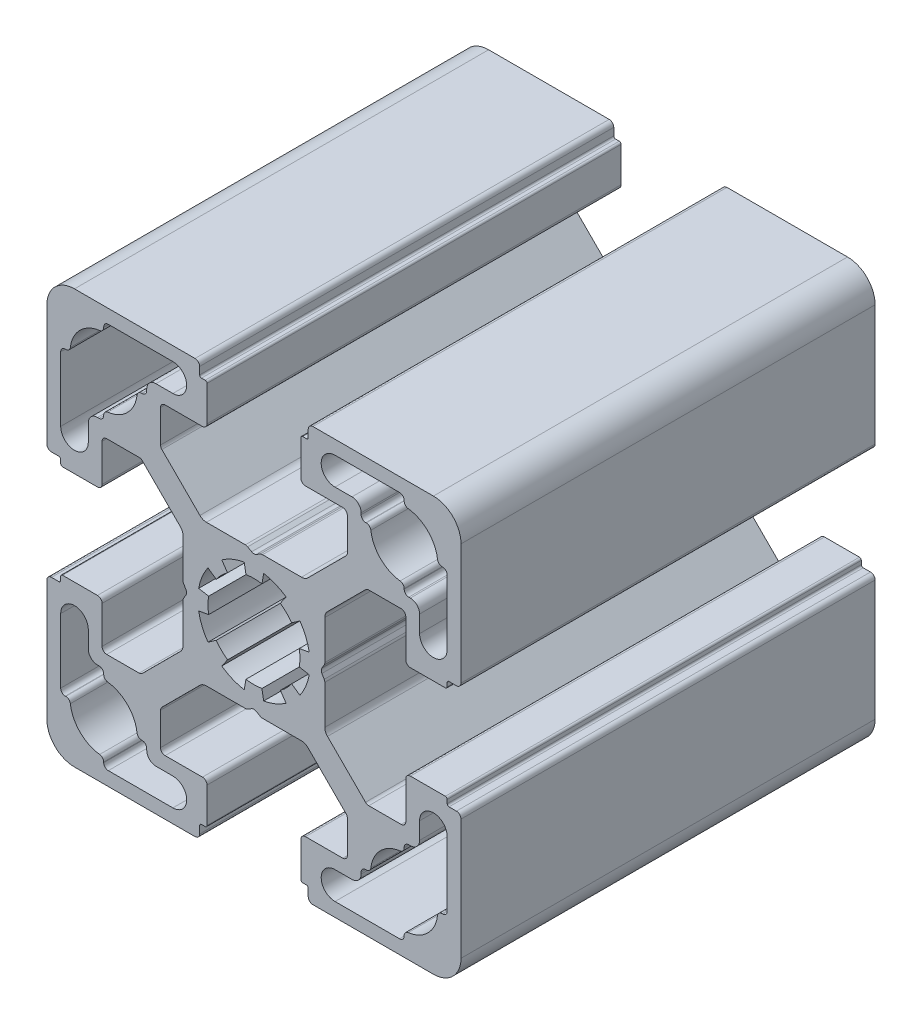
SolidWorks part; units mm, degrees
material "АД31Т ГОСТ 4784-97"
ref_plane "Спереди" through (0, 0, 0) normal (0, 0, 1) x (1, 0, 0)
ref_plane "Сверху" through (0, 0, 0) normal (0, 1, 0) x (1, 0, 0)
ref_plane "Справа" through (0, 0, 0) normal (1, 0, 0) x (0, 0, -1)
sketch "Эскиз1" plane through (0, 0, 0) normal (0, 0, 1) x (1, 0, 0)
  line L0 (-21, 15.825) -> (-21, 8.808)
  line L1 (-15.825, -21) -> (-8.808, -21)
  line L2 (-7.7005, 0.9291) -> (-7.7005, 5.1649)
  line L4 (15.825, 21) -> (8.808, 21)
  line L5 (5.6, 16.5) -> (9.65, 16.5)
  line L6 (16.325, 20.4448) -> (16.325, 20.5)
  line L7 (10.65, 18) -> (8.808, 18)
  line L8 (-7.3858, -0.25) -> (-7.618, -0.6523)
  line L9 (-2.8679, 4.0958) -> (-3.4988, 4.9968)
  line L10 (-16.5, 5.6) -> (-16.5, 9.65)
  line L11 (-16, 10.15) -> (-12.4784, 10.15)
  line L12 (-22, 5.9) -> (-21.2, 5.9)
  line L13 (-20.8, 5.1) -> (-17, 5.1)
  line L14 (-21, 5.7) -> (-21, 5.3)
  line L15 (-22, 5.9) -> (-21.2, 5.9)
  line L16 (4.0958, 2.8679) -> (4.9968, 3.4988)
  line L17 (4.0958, 2.8679) -> (4.9968, 3.4988)
  line L18 (-21, 5.7) -> (-21, 5.3)
  line L19 (-8.1188, 10.2401) -> (-5.8721, 7.9934)
  line L20 (0.9291, 7.7005) -> (5.1649, 7.7005)
  line L21 (-22.5, 6.4) -> (-22.5, 19.5)
  line L22 (10.15, 16) -> (10.15, 12.4784)
  line L23 (0.25, 7.3858) -> (0.6791, 7.6335)
  line L24 (16.325, 12.2052) -> (16.325, 12.15)
  line L25 (-6.4, 22.5) -> (-19.5, 22.5)
  line L26 (16.825, 11.65) -> (17, 11.65)
  line L27 (-10.2401, 8.1188) -> (-12.1249, 10.0036)
  line L28 (-5.7, 21) -> (-5.3, 21)
  line L29 (-7.3858, 0.25) -> (-7.6335, 0.6791)
  line L30 (-0.25, 7.3858) -> (-0.6791, 7.6335)
  line L31 (-5.9, 22) -> (-5.9, 21.2)
  line L32 (-5.7, 21) -> (-5.3, 21)
  line L33 (-5.1, 20.8) -> (-5.1, 17)
  line L34 (-5.9, 22) -> (-5.9, 21.2)
  line L35 (-8.1188, 10.2401) -> (-10.0036, 12.1249)
  line L36 (-5.6, 16.5) -> (-9.65, 16.5)
  line L37 (-10.2401, 8.1188) -> (-7.9934, 5.8721)
  line L38 (18, 10.65) -> (18, 8.808)
  line L39 (-12.2052, 16.325) -> (-12.15, 16.325)
  line L40 (-20.4448, 16.325) -> (-20.5, 16.325)
  line L41 (11.65, 16.825) -> (11.65, 17)
  line L42 (-11.65, 16.825) -> (-11.65, 17)
  line L43 (-18, 10.65) -> (-18, 8.808)
  line L44 (-16.825, 11.65) -> (-17, 11.65)
  line L45 (20.4448, 16.325) -> (20.5, 16.325)
  line L46 (-16.325, 12.2052) -> (-16.325, 12.15)
  line L47 (12.2052, 16.325) -> (12.15, 16.325)
  line L48 (10.2401, 8.1188) -> (7.9934, 5.8721)
  line L49 (0.25, 7.3858) -> (0.6523, 7.618)
  line L50 (-0.9291, 7.7005) -> (-5.1649, 7.7005)
  line L51 (5.6, 16.5) -> (9.65, 16.5)
  line L52 (8.1188, 10.2401) -> (10.0036, 12.1249)
  line L53 (5.9, 22) -> (5.9, 21.2)
  line L54 (5.1, 20.8) -> (5.1, 17)
  line L55 (-0.9291, -7.7005) -> (-5.1649, -7.7005)
  line L56 (5.7, 21) -> (5.3, 21)
  line L57 (5.9, 22) -> (5.9, 21.2)
  line L58 (-0.25, -7.3858) -> (-0.6791, -7.6335)
  line L59 (5.7, 21) -> (5.3, 21)
  line L60 (10.2401, 8.1188) -> (12.1249, 10.0036)
  line L61 (6.4, 22.5) -> (19.5, 22.5)
  line L62 (22.5, 6.4) -> (22.5, 19.5)
  line L63 (-10.15, 16) -> (-10.15, 12.4784)
  line L64 (8.1188, 10.2401) -> (5.8721, 7.9934)
  line L65 (0.25, -7.3858) -> (0.6791, -7.6335)
  line L66 (21, 5.7) -> (21, 5.3)
  line L67 (-0.25, -7.3858) -> (-0.6523, -7.618)
  line L68 (22, 5.9) -> (21.2, 5.9)
  line L69 (21, 5.7) -> (21, 5.3)
  line L70 (20.8, 5.1) -> (17, 5.1)
  line L71 (22, 5.9) -> (21.2, 5.9)
  line L72 (16, 10.15) -> (12.4784, 10.15)
  line L73 (16.5, 5.6) -> (16.5, 9.65)
  line L74 (-0.9291, 7.7005) -> (-5.1649, 7.7005)
  line L75 (2.8679, 4.0958) -> (3.4988, 4.9968)
  line L76 (7.7005, 0.9291) -> (7.7005, 5.1649)
  line L77 (0.9291, -7.7005) -> (5.1649, -7.7005)
  line L78 (21, 15.825) -> (21, 8.808)
  line L79 (-5.6, -16.5) -> (-9.65, -16.5)
  line L80 (-16.325, -20.4448) -> (-16.325, -20.5)
  line L81 (4.0958, -2.8679) -> (4.9968, -3.4988)
  line L82 (2.8679, -4.0958) -> (3.4988, -4.9968)
  line L83 (-10.65, -18) -> (-8.808, -18)
  line L84 (4.0958, -2.8679) -> (4.9968, -3.4988)
  line L85 (2.8679, -4.0958) -> (3.4988, -4.9968)
  line L86 (0.8682, -4.924) -> (1.0593, -6.0073)
  line L87 (0.8682, -4.924) -> (1.0593, -6.0073)
  line L88 (-0.8682, -4.924) -> (-1.0593, -6.0073)
  line L89 (-4.0958, -2.8679) -> (-4.9968, -3.4988)
  line L90 (-0.8682, -4.924) -> (-1.0593, -6.0073)
  line L91 (-4.0958, -2.8679) -> (-4.9968, -3.4988)
  line L92 (21, -15.825) -> (21, -8.808)
  line L93 (2.8679, -4.0958) -> (3.4988, -4.9968)
  line L94 (-0.9291, -7.7005) -> (-5.1649, -7.7005)
  line L95 (16.5, -5.6) -> (16.5, -9.65)
  line L96 (16, -10.15) -> (12.4784, -10.15)
  line L97 (22, -5.9) -> (21.2, -5.9)
  line L98 (20.8, -5.1) -> (17, -5.1)
  line L99 (21, -5.7) -> (21, -5.3)
  line L100 (22, -5.9) -> (21.2, -5.9)
  line L101 (21, -5.7) -> (21, -5.3)
  line L102 (8.1188, -10.2401) -> (5.8721, -7.9934)
  line L103 (-7.3858, -0.25) -> (-7.6335, -0.6791)
  line L104 (-10.15, -16) -> (-10.15, -12.4784)
  line L105 (22.5, -6.4) -> (22.5, -19.5)
  line L106 (6.4, -22.5) -> (19.5, -22.5)
  line L107 (10.2401, -8.1188) -> (12.1249, -10.0036)
  line L108 (5.7, -21) -> (5.3, -21)
  line L109 (7.7005, -0.9291) -> (7.7005, -5.1649)
  line L110 (5.9, -22) -> (5.9, -21.2)
  line L111 (5.7, -21) -> (5.3, -21)
  line L112 (7.3858, 0.25) -> (7.618, 0.6523)
  line L113 (5.1, -20.8) -> (5.1, -17)
  line L114 (5.9, -22) -> (5.9, -21.2)
  line L115 (-7.7005, -0.9291) -> (-7.7005, -5.1649)
  line L116 (8.1188, -10.2401) -> (10.0036, -12.1249)
  line L117 (5.6, -16.5) -> (9.65, -16.5)
  line L118 (-0.9291, -7.7005) -> (-5.1649, -7.7005)
  line L119 (0.25, -7.3858) -> (0.6523, -7.618)
  line L120 (10.2401, -8.1188) -> (7.9934, -5.8721)
  line L121 (12.2052, -16.325) -> (12.15, -16.325)
  line L122 (-16.325, -12.2052) -> (-16.325, -12.15)
  line L123 (7.3858, -0.25) -> (7.6335, -0.6791)
  line L124 (20.4448, -16.325) -> (20.5, -16.325)
  line L125 (-16.825, -11.65) -> (-17, -11.65)
  line L126 (-18, -10.65) -> (-18, -8.808)
  line L127 (-11.65, -16.825) -> (-11.65, -17)
  line L128 (11.65, -16.825) -> (11.65, -17)
  line L129 (-20.4448, -16.325) -> (-20.5, -16.325)
  line L130 (-4.0958, 2.8679) -> (-4.9968, 3.4988)
  line L131 (-0.8682, 4.924) -> (-1.0593, 6.0073)
  line L132 (0.8682, 4.924) -> (1.0593, 6.0073)
  line L133 (-10.65, 18) -> (-8.808, 18)
  line L134 (-4.924, -0.8682) -> (-6.0073, -1.0593)
  line L135 (-4.924, 0.8682) -> (-6.0073, 1.0593)
  line L136 (0.8682, -4.924) -> (1.0593, -6.0073)
  line L137 (-0.8682, -4.924) -> (-1.0593, -6.0073)
  line L138 (-2.8679, -4.0958) -> (-3.4988, -4.9968)
  line L139 (-4.0958, -2.8679) -> (-4.9968, -3.4988)
  line L140 (-4.924, -0.8682) -> (-6.0073, -1.0593)
  line L141 (-4.924, 0.8682) -> (-6.0073, 1.0593)
  line L142 (2.8679, 4.0958) -> (3.4988, 4.9968)
  line L143 (4.0958, 2.8679) -> (4.9968, 3.4988)
  line L144 (4.924, 0.8682) -> (6.0073, 1.0593)
  line L145 (4.924, -0.8682) -> (6.0073, -1.0593)
  line L146 (4.0958, -2.8679) -> (4.9968, -3.4988)
  line L147 (2.8679, -4.0958) -> (3.4988, -4.9968)
  line L148 (-16.325, 20.4448) -> (-16.325, 20.5)
  line L149 (-12.2052, -16.325) -> (-12.15, -16.325)
  line L150 (-5.6, 16.5) -> (-9.65, 16.5)
  line L151 (-15.825, 21) -> (-8.808, 21)
  line L152 (18, -10.65) -> (18, -8.808)
  line L153 (-10.2401, -8.1188) -> (-7.9934, -5.8721)
  line L154 (-5.6, -16.5) -> (-9.65, -16.5)
  line L155 (-8.1188, -10.2401) -> (-10.0036, -12.1249)
  line L156 (-5.9, -22) -> (-5.9, -21.2)
  line L157 (-5.1, -20.8) -> (-5.1, -17)
  line L158 (-5.7, -21) -> (-5.3, -21)
  line L159 (-5.9, -22) -> (-5.9, -21.2)
  line L160 (-0.25, -7.3858) -> (-0.6791, -7.6335)
  line L161 (-5.7, -21) -> (-5.3, -21)
  line L162 (-10.2401, -8.1188) -> (-12.1249, -10.0036)
  line L163 (16.825, -11.65) -> (17, -11.65)
  line L164 (-6.4, -22.5) -> (-19.5, -22.5)
  line L165 (16.325, -12.2052) -> (16.325, -12.15)
  line L166 (0.25, -7.3858) -> (0.6791, -7.6335)
  line L167 (10.15, -16) -> (10.15, -12.4784)
  line L168 (7.3858, 0.25) -> (7.6335, 0.6791)
  line L169 (-22.5, -6.4) -> (-22.5, -19.5)
  line L170 (0.9291, -7.7005) -> (5.1649, -7.7005)
  line L171 (7.7005, 0.9291) -> (7.7005, 5.1649)
  line L172 (-8.1188, -10.2401) -> (-5.8721, -7.9934)
  line L173 (-21, -5.7) -> (-21, -5.3)
  line L174 (4.0958, -2.8679) -> (4.9968, -3.4988)
  line L175 (4.0958, -2.8679) -> (4.9968, -3.4988)
  line L176 (4.0958, -2.8679) -> (4.9968, -3.4988)
  line L177 (-22, -5.9) -> (-21.2, -5.9)
  line L178 (-21, -5.7) -> (-21, -5.3)
  line L179 (-20.8, -5.1) -> (-17, -5.1)
  line L180 (-22, -5.9) -> (-21.2, -5.9)
  line L181 (-16, -10.15) -> (-12.4784, -10.15)
  line L182 (-2.8679, -4.0958) -> (-3.4988, -4.9968)
  line L183 (-16.5, -5.6) -> (-16.5, -9.65)
  line L184 (-2.8679, -4.0958) -> (-3.4988, -4.9968)
  line L185 (10.65, -18) -> (8.808, -18)
  line L186 (16.325, -20.4448) -> (16.325, -20.5)
  line L187 (5.6, -16.5) -> (9.65, -16.5)
  line L188 (15.825, -21) -> (8.808, -21)
  line L189 (-21, -15.825) -> (-21, -8.808)
  arc A0 (-2.8679, 4.0958) -> (-4.0958, 2.8679) centre (0, 0) ccw
  arc A1 (-4.9968, 3.4988) -> (-6.0073, 1.0593) centre (0, 0) ccw
  arc A2 (-19.5, 22.5) -> (-22.5, 19.5) centre (-19.5, 19.5) ccw
  arc A3 (-12.1249, 10.0036) -> (-12.4784, 10.15) centre (-12.4784, 9.65) ccw
  arc A4 (-16, 10.15) -> (-16.5, 9.65) centre (-16, 9.65) ccw
  arc A5 (-17, 5.1) -> (-16.5, 5.6) centre (-17, 5.6) ccw
  arc A6 (-22.5, 6.4) -> (-22, 5.9) centre (-22, 6.4) ccw
  arc A7 (-20.8, 5.1) -> (-21, 5.3) centre (-20.8, 5.3) cw
  arc A8 (-21.2, 5.9) -> (-21, 5.7) centre (-21.2, 5.7) cw
  arc A9 (-7.9934, 5.8721) -> (-7.7005, 5.1649) centre (-8.7005, 5.1649) cw
  arc A10 (10.15, 16) -> (9.65, 16.5) centre (9.65, 16) ccw
  arc A11 (8.808, 21) -> (8.808, 18) centre (8.808, 19.5) ccw
  arc A12 (11.65, 17) -> (10.65, 18) centre (10.65, 17) ccw
  arc A13 (16.325, 20.5) -> (15.825, 21) centre (15.825, 20.5) ccw
  arc A14 (16.325, 20.4448) -> (16.7648, 19.9484) centre (16.825, 20.4448) ccw
  arc A15 (12.2052, 16.325) -> (12.7016, 15.8852) centre (12.2052, 15.825) cw
  arc A16 (-7.6335, -0.6791) -> (-7.7005, -0.9291) centre (-7.2005, -0.9291) ccw
  arc A17 (-5.9, 21.2) -> (-5.7, 21) centre (-5.7, 21.2) ccw
  arc A18 (-7.3858, -0.25) -> (-7.3858, 0.25) centre (-7.8188, 0) ccw
  arc A19 (-22.5, 6.4) -> (-22, 5.9) centre (-22, 6.4) ccw
  arc A20 (-21.2, 5.9) -> (-21, 5.7) centre (-21.2, 5.7) cw
  arc A21 (-6.4, 22.5) -> (-5.9, 22) centre (-6.4, 22) cw
  arc A22 (-0.6791, 7.6335) -> (-0.9291, 7.7005) centre (-0.9291, 7.2005) ccw
  arc A23 (12.15, 16.325) -> (11.65, 16.825) centre (12.15, 16.825) cw
  arc A24 (0.25, 7.3858) -> (-0.25, 7.3858) centre (0, 7.8188) cw
  arc A25 (-5.9, 21.2) -> (-5.7, 21) centre (-5.7, 21.2) ccw
  arc A26 (-5.1, 20.8) -> (-5.3, 21) centre (-5.3, 20.8) ccw
  arc A27 (-6.4, 22.5) -> (-5.9, 22) centre (-6.4, 22) cw
  arc A28 (-5.1, 17) -> (-5.6, 16.5) centre (-5.6, 17) cw
  arc A29 (-10.15, 16) -> (-9.65, 16.5) centre (-9.65, 16) cw
  arc A30 (-5.8721, 7.9934) -> (-5.1649, 7.7005) centre (-5.1649, 8.7005) ccw
  arc A31 (-15.8852, 12.7016) -> (-12.7016, 15.8852) centre (-16.325, 16.325) ccw
  arc A32 (-21, 8.808) -> (-18, 8.808) centre (-19.5, 8.808) ccw
  arc A33 (-17, 11.65) -> (-18, 10.65) centre (-17, 10.65) ccw
  arc A34 (-20.5, 16.325) -> (-21, 15.825) centre (-20.5, 15.825) ccw
  arc A35 (-20.4448, 16.325) -> (-19.9484, 16.7648) centre (-20.4448, 16.825) ccw
  arc A36 (-16.325, 12.2052) -> (-15.8852, 12.7016) centre (-15.825, 12.2052) cw
  arc A37 (16.7648, 19.9484) -> (19.9484, 16.7648) centre (16.325, 16.325) cw
  arc A38 (16.325, 12.15) -> (16.825, 11.65) centre (16.825, 12.15) ccw
  arc A39 (19.5, 22.5) -> (22.5, 19.5) centre (19.5, 19.5) cw
  arc A40 (10.0036, 12.1249) -> (10.15, 12.4784) centre (9.65, 12.4784) ccw
  arc A41 (16.325, 12.2052) -> (15.8852, 12.7016) centre (15.825, 12.2052) ccw
  arc A42 (20.4448, 16.325) -> (19.9484, 16.7648) centre (20.4448, 16.825) cw
  arc A43 (0.6791, 7.6335) -> (0.9291, 7.7005) centre (0.9291, 7.2005) cw
  arc A44 (-10.0036, 12.1249) -> (-10.15, 12.4784) centre (-9.65, 12.4784) cw
  arc A45 (20.5, 16.325) -> (21, 15.825) centre (20.5, 15.825) cw
  arc A46 (17, 11.65) -> (18, 10.65) centre (17, 10.65) cw
  arc A47 (21, 8.808) -> (18, 8.808) centre (19.5, 8.808) cw
  arc A48 (0.6791, -7.6335) -> (0.9291, -7.7005) centre (0.9291, -7.2005) ccw
  arc A49 (15.8852, 12.7016) -> (12.7016, 15.8852) centre (16.325, 16.325) cw
  arc A50 (5.8721, 7.9934) -> (5.1649, 7.7005) centre (5.1649, 8.7005) cw
  arc A51 (-0.25, -7.3858) -> (0.25, -7.3858) centre (0, -7.8188) cw
  arc A52 (10.15, 16) -> (9.65, 16.5) centre (9.65, 16) ccw
  arc A53 (5.1, 17) -> (5.6, 16.5) centre (5.6, 17) ccw
  arc A54 (6.4, 22.5) -> (5.9, 22) centre (6.4, 22) ccw
  arc A55 (5.1, 20.8) -> (5.3, 21) centre (5.3, 20.8) cw
  arc A56 (5.9, 21.2) -> (5.7, 21) centre (5.7, 21.2) cw
  arc A57 (6.4, 22.5) -> (5.9, 22) centre (6.4, 22) ccw
  arc A58 (-0.6791, -7.6335) -> (-0.9291, -7.7005) centre (-0.9291, -7.2005) cw
  arc A59 (21.2, 5.9) -> (21, 5.7) centre (21.2, 5.7) ccw
  arc A60 (22.5, 6.4) -> (22, 5.9) centre (22, 6.4) cw
  arc A61 (5.9, 21.2) -> (5.7, 21) centre (5.7, 21.2) cw
  arc A62 (7.9934, 5.8721) -> (7.7005, 5.1649) centre (8.7005, 5.1649) ccw
  arc A63 (21.2, 5.9) -> (21, 5.7) centre (21.2, 5.7) ccw
  arc A64 (20.8, 5.1) -> (21, 5.3) centre (20.8, 5.3) ccw
  arc A65 (22.5, 6.4) -> (22, 5.9) centre (22, 6.4) cw
  arc A66 (17, 5.1) -> (16.5, 5.6) centre (17, 5.6) cw
  arc A67 (7.6335, 0.6791) -> (7.7005, 0.9291) centre (7.2005, 0.9291) ccw
  arc A68 (16, 10.15) -> (16.5, 9.65) centre (16, 9.65) cw
  arc A69 (12.1249, 10.0036) -> (12.4784, 10.15) centre (12.4784, 9.65) cw
  arc A70 (19.5, 22.5) -> (22.5, 19.5) centre (19.5, 19.5) cw
  arc A71 (4.9968, 3.4988) -> (6.0073, 1.0593) centre (0, 0) cw
  arc A72 (7.3858, 0.25) -> (7.3858, -0.25) centre (7.8188, 0) ccw
  arc A73 (2.8679, 4.0958) -> (4.0958, 2.8679) centre (0, 0) cw
  arc A74 (-10.15, -16) -> (-9.65, -16.5) centre (-9.65, -16) ccw
  arc A75 (-8.808, -21) -> (-8.808, -18) centre (-8.808, -19.5) ccw
  arc A76 (-11.65, -17) -> (-10.65, -18) centre (-10.65, -17) ccw
  arc A77 (-16.325, -20.5) -> (-15.825, -21) centre (-15.825, -20.5) ccw
  arc A78 (-16.325, -20.4448) -> (-16.7648, -19.9484) centre (-16.825, -20.4448) ccw
  arc A79 (-12.2052, -16.325) -> (-12.7016, -15.8852) centre (-12.2052, -15.825) cw
  arc A80 (-12.15, -16.325) -> (-11.65, -16.825) centre (-12.15, -16.825) cw
  arc A81 (-16.7648, -19.9484) -> (-19.9484, -16.7648) centre (-16.325, -16.325) cw
  arc A82 (-16.325, -12.15) -> (-16.825, -11.65) centre (-16.825, -12.15) ccw
  arc A83 (-19.5, -22.5) -> (-22.5, -19.5) centre (-19.5, -19.5) cw
  arc A84 (4.0958, -2.8679) -> (2.8679, -4.0958) centre (0, 0) cw
  arc A85 (3.4988, -4.9968) -> (1.0593, -6.0073) centre (0, 0) cw
  arc A86 (0.8682, -4.924) -> (-0.8682, -4.924) centre (0, 0) cw
  arc A87 (-1.0593, -6.0073) -> (-3.4988, -4.9968) centre (0, 0) cw
  arc A88 (3.4988, -4.9968) -> (1.0593, -6.0073) centre (0, 0) cw
  arc A89 (0.8682, -4.924) -> (-0.8682, -4.924) centre (0, 0) cw
  arc A90 (-1.0593, -6.0073) -> (-3.4988, -4.9968) centre (0, 0) cw
  arc A91 (2.8679, -4.0958) -> (4.0958, -2.8679) centre (0, 0) ccw
  arc A92 (7.6335, -0.6791) -> (7.7005, -0.9291) centre (7.2005, -0.9291) cw
  arc A93 (19.5, -22.5) -> (22.5, -19.5) centre (19.5, -19.5) ccw
  arc A94 (12.1249, -10.0036) -> (12.4784, -10.15) centre (12.4784, -9.65) ccw
  arc A95 (16, -10.15) -> (16.5, -9.65) centre (16, -9.65) ccw
  arc A96 (17, -5.1) -> (16.5, -5.6) centre (17, -5.6) ccw
  arc A97 (22.5, -6.4) -> (22, -5.9) centre (22, -6.4) ccw
  arc A98 (20.8, -5.1) -> (21, -5.3) centre (20.8, -5.3) cw
  arc A99 (21.2, -5.9) -> (21, -5.7) centre (21.2, -5.7) cw
  arc A100 (7.9934, -5.8721) -> (7.7005, -5.1649) centre (8.7005, -5.1649) cw
  arc A101 (5.9, -21.2) -> (5.7, -21) centre (5.7, -21.2) ccw
  arc A102 (-7.6335, 0.6791) -> (-7.7005, 0.9291) centre (-7.2005, 0.9291) cw
  arc A103 (22.5, -6.4) -> (22, -5.9) centre (22, -6.4) ccw
  arc A104 (21.2, -5.9) -> (21, -5.7) centre (21.2, -5.7) cw
  arc A105 (6.4, -22.5) -> (5.9, -22) centre (6.4, -22) cw
  arc A106 (5.9, -21.2) -> (5.7, -21) centre (5.7, -21.2) ccw
  arc A107 (5.1, -20.8) -> (5.3, -21) centre (5.3, -20.8) ccw
  arc A108 (6.4, -22.5) -> (5.9, -22) centre (6.4, -22) cw
  arc A109 (5.1, -17) -> (5.6, -16.5) centre (5.6, -17) cw
  arc A110 (10.15, -16) -> (9.65, -16.5) centre (9.65, -16) cw
  arc A111 (5.8721, -7.9934) -> (5.1649, -7.7005) centre (5.1649, -8.7005) ccw
  arc A112 (15.8852, -12.7016) -> (12.7016, -15.8852) centre (16.325, -16.325) ccw
  arc A113 (21, -8.808) -> (18, -8.808) centre (19.5, -8.808) ccw
  arc A114 (-1.0593, 6.0073) -> (-3.4988, 4.9968) centre (0, 0) ccw
  arc A115 (0.8682, 4.924) -> (-0.8682, 4.924) centre (0, 0) ccw
  arc A116 (3.4988, 4.9968) -> (1.0593, 6.0073) centre (0, 0) ccw
  arc A117 (4.0958, 2.8679) -> (2.8679, 4.0958) centre (0, 0) ccw
  arc A118 (4.924, -0.8682) -> (4.924, 0.8682) centre (0, 0) ccw
  arc A119 (6.0073, 1.0593) -> (4.9968, 3.4988) centre (0, 0) ccw
  arc A120 (2.8679, -4.0958) -> (4.0958, -2.8679) centre (0, 0) ccw
  arc A121 (4.9968, -3.4988) -> (6.0073, -1.0593) centre (0, 0) ccw
  arc A122 (-0.8682, -4.924) -> (0.8682, -4.924) centre (0, 0) ccw
  arc A123 (1.0593, -6.0073) -> (3.4988, -4.9968) centre (0, 0) ccw
  arc A124 (-4.0958, -2.8679) -> (-2.8679, -4.0958) centre (0, 0) ccw
  arc A125 (-3.4988, -4.9968) -> (-1.0593, -6.0073) centre (0, 0) ccw
  arc A126 (-4.924, 0.8682) -> (-4.924, -0.8682) centre (0, 0) ccw
  arc A127 (-6.0073, -1.0593) -> (-4.9968, -3.4988) centre (0, 0) ccw
  arc A128 (-19.5, 22.5) -> (-22.5, 19.5) centre (-19.5, 19.5) ccw
  arc A129 (-16.325, 12.15) -> (-16.825, 11.65) centre (-16.825, 12.15) cw
  arc A130 (-16.7648, 19.9484) -> (-19.9484, 16.7648) centre (-16.325, 16.325) ccw
  arc A131 (-12.15, 16.325) -> (-11.65, 16.825) centre (-12.15, 16.825) ccw
  arc A132 (-12.2052, 16.325) -> (-12.7016, 15.8852) centre (-12.2052, 15.825) ccw
  arc A133 (-16.325, 20.4448) -> (-16.7648, 19.9484) centre (-16.825, 20.4448) cw
  arc A134 (-16.325, 20.5) -> (-15.825, 21) centre (-15.825, 20.5) cw
  arc A135 (-11.65, 17) -> (-10.65, 18) centre (-10.65, 17) cw
  arc A136 (-8.808, 21) -> (-8.808, 18) centre (-8.808, 19.5) cw
  arc A137 (-10.15, 16) -> (-9.65, 16.5) centre (-9.65, 16) cw
  arc A138 (17, -11.65) -> (18, -10.65) centre (17, -10.65) ccw
  arc A139 (20.5, -16.325) -> (21, -15.825) centre (20.5, -15.825) ccw
  arc A140 (-10.0036, -12.1249) -> (-10.15, -12.4784) centre (-9.65, -12.4784) ccw
  arc A141 (0.6791, -7.6335) -> (0.9291, -7.7005) centre (0.9291, -7.2005) ccw
  arc A142 (20.4448, -16.325) -> (19.9484, -16.7648) centre (20.4448, -16.825) ccw
  arc A143 (16.325, -12.2052) -> (15.8852, -12.7016) centre (15.825, -12.2052) cw
  arc A144 (10.0036, -12.1249) -> (10.15, -12.4784) centre (9.65, -12.4784) cw
  arc A145 (19.5, -22.5) -> (22.5, -19.5) centre (19.5, -19.5) ccw
  arc A146 (16.325, -12.15) -> (16.825, -11.65) centre (16.825, -12.15) cw
  arc A147 (16.7648, -19.9484) -> (19.9484, -16.7648) centre (16.325, -16.325) ccw
  arc A148 (-16.325, -12.2052) -> (-15.8852, -12.7016) centre (-15.825, -12.2052) ccw
  arc A149 (-20.4448, -16.325) -> (-19.9484, -16.7648) centre (-20.4448, -16.825) cw
  arc A150 (-20.5, -16.325) -> (-21, -15.825) centre (-20.5, -15.825) cw
  arc A151 (-17, -11.65) -> (-18, -10.65) centre (-17, -10.65) cw
  arc A152 (-21, -8.808) -> (-18, -8.808) centre (-19.5, -8.808) cw
  arc A153 (-15.8852, -12.7016) -> (-12.7016, -15.8852) centre (-16.325, -16.325) cw
  arc A154 (-5.8721, -7.9934) -> (-5.1649, -7.7005) centre (-5.1649, -8.7005) cw
  arc A155 (-10.15, -16) -> (-9.65, -16.5) centre (-9.65, -16) ccw
  arc A156 (-5.1, -17) -> (-5.6, -16.5) centre (-5.6, -17) ccw
  arc A157 (-6.4, -22.5) -> (-5.9, -22) centre (-6.4, -22) ccw
  arc A158 (-5.1, -20.8) -> (-5.3, -21) centre (-5.3, -20.8) cw
  arc A159 (-5.9, -21.2) -> (-5.7, -21) centre (-5.7, -21.2) cw
  arc A160 (0.25, -7.3858) -> (-0.25, -7.3858) centre (0, -7.8188) ccw
  arc A161 (12.15, -16.325) -> (11.65, -16.825) centre (12.15, -16.825) ccw
  arc A162 (-0.6791, -7.6335) -> (-0.9291, -7.7005) centre (-0.9291, -7.2005) cw
  arc A163 (-6.4, -22.5) -> (-5.9, -22) centre (-6.4, -22) ccw
  arc A164 (-21.2, -5.9) -> (-21, -5.7) centre (-21.2, -5.7) ccw
  arc A165 (-22.5, -6.4) -> (-22, -5.9) centre (-22, -6.4) cw
  arc A166 (-5.9, -21.2) -> (-5.7, -21) centre (-5.7, -21.2) cw
  arc A167 (12.2052, -16.325) -> (12.7016, -15.8852) centre (12.2052, -15.825) ccw
  arc A168 (16.325, -20.4448) -> (16.7648, -19.9484) centre (16.825, -20.4448) cw
  arc A169 (16.325, -20.5) -> (15.825, -21) centre (15.825, -20.5) cw
  arc A170 (11.65, -17) -> (10.65, -18) centre (10.65, -17) cw
  arc A171 (8.808, -21) -> (8.808, -18) centre (8.808, -19.5) cw
  arc A172 (10.15, -16) -> (9.65, -16.5) centre (9.65, -16) cw
  arc A173 (-7.9934, -5.8721) -> (-7.7005, -5.1649) centre (-8.7005, -5.1649) ccw
  arc A174 (-21.2, -5.9) -> (-21, -5.7) centre (-21.2, -5.7) ccw
  arc A175 (-20.8, -5.1) -> (-21, -5.3) centre (-20.8, -5.3) ccw
  arc A176 (-22.5, -6.4) -> (-22, -5.9) centre (-22, -6.4) cw
  arc A177 (-17, -5.1) -> (-16.5, -5.6) centre (-17, -5.6) cw
  arc A178 (-16, -10.15) -> (-16.5, -9.65) centre (-16, -9.65) cw
  arc A179 (-12.1249, -10.0036) -> (-12.4784, -10.15) centre (-12.4784, -9.65) cw
  arc A180 (-19.5, -22.5) -> (-22.5, -19.5) centre (-19.5, -19.5) cw
  arc A181 (-2.8679, -4.0958) -> (-4.0958, -2.8679) centre (0, 0) cw
  point P69 (-7.7414, 0.866)
  point P73 (-22.5, 5.9)
  point P96 (-5.9, 22.5)
  point P102 (-12.675, 16.325)
  point P115 (-19.975, 16.325)
  point P143 (0.866, 7.7414)
  point P144 (-0.866, 7.7414)
  point P190 (16.325, 19.975)
  point P191 (16.325, 12.675)
  point P194 (19.975, 16.325)
  point P195 (12.675, 16.325)
  point P196 (5.9, 22.5)
  point P197 (22.5, 5.9)
  point P259 (-0.866, -7.7414)
  point P275 (-7.7414, -0.866)
  point P308 (0.866, -7.7414)
  point P346 (-16.325, 12.675)
  point P365 (-16.325, 19.975)
  point P428 (-16.325, -19.975)
  point P429 (-16.325, -12.675)
  point P430 (22.5, -5.9)
  point P432 (5.9, -22.5)
  point P439 (12.675, -16.325)
  point P440 (19.975, -16.325)
  point P441 (16.325, -12.675)
  point P446 (7.7414, -0.866)
  point P447 (7.7414, 0.866)
  point P448 (16.325, -19.975)
  point P449 (-19.975, -16.325)
  point P450 (-12.675, -16.325)
  point P451 (-5.9, -22.5)
  point P452 (-22.5, -5.9)
extrude "Бобышка-Вытянуть4" add sketch "Эскиз1" along normal blind 45 contours L162 A179 L181 A178 L183 A177 L179 A175 L173 A164 L177 A165 L169 A83 L164 A157 L156 A159 L158 A158 L157 A156 L79 A74 L104 A140 L155 L172 A154 L55 A58 L58 A51 L65 A48 L77 A111 L102 L116 A144 L167 A110 L117 A109 L113 A107 L108 A101 L110
